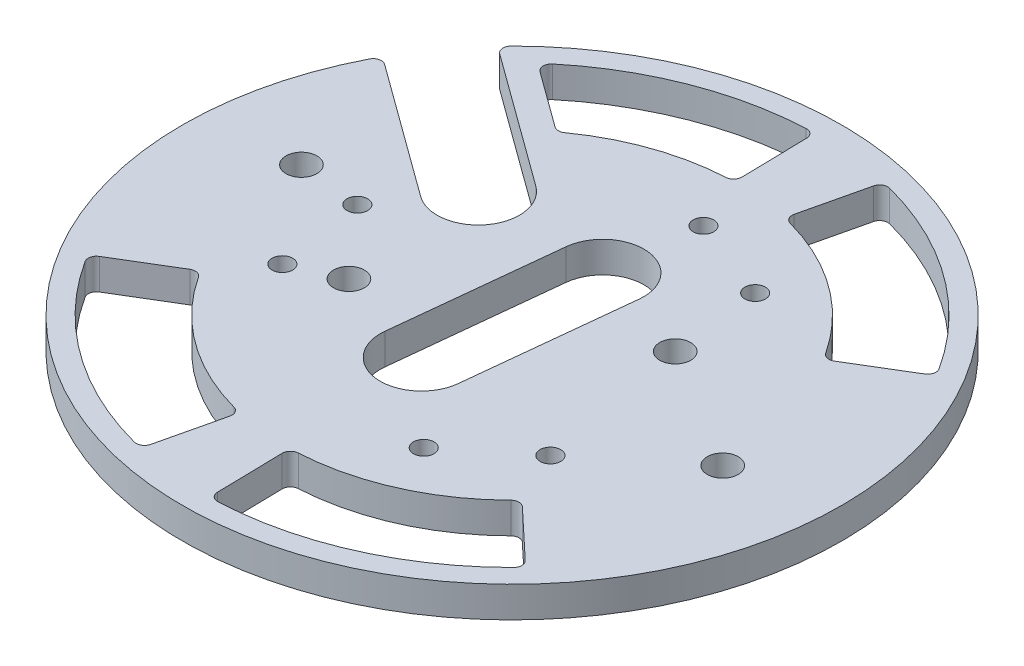
SolidWorks part; units mm, degrees
ref_plane "Front Plane" through (0, 0, 0) normal (0, 0, 1) x (1, 0, 0)
ref_plane "Top Plane" through (0, 0, 0) normal (0, 1, 0) x (1, 0, 0)
ref_plane "Right Plane" through (0, 0, 0) normal (1, 0, 0) x (0, 0, -1)
sketch "Sketch1" plane through (0, 0, 0) normal (0, 1, 0) x (1, 0, 0)
  circle A0 centre (0, 0) radius 101.6
extrude "Boss-Extrude1" add sketch "Sketch1" along normal blind 9.525
sketch "Sketch2" plane through (0, 9.525, 0) normal (0, 1, 0) x (1, 0, 0)
  line L0 (0, 0) -> (34.8175, 15.4709)
  line L1 (0, 60.325) -> (12.6294, 58.9882)
  line L2 (0, 60.325) -> (12.6294, 58.9882)
  line L3 (0, 60.325) -> (-1.3368, 47.6956)
  line L4 (12.6294, 58.9882) -> (11.2926, 46.3587)
  line L5 (-1.3368, 47.6956) -> (11.2926, 46.3587)
  line L6 (0, 0) -> (-34.8175, -15.4709)
  line L7 (0, 0) -> (5.6463, 53.3419)
  line L8 (5.6463, 53.3419) -> (6.6842, 63.1472)
  line L9 (6.6842, 63.1472) -> (6.9516, 65.6731)
  line L10 (0, 0) -> (5.6463, 53.3419)
  line L11 (6.6842, 63.1472) -> (6.9516, 65.6731)
  line L12 (6.9516, 65.6731) -> (10.6947, 101.0356)
  line L13 (4.9779, 47.0271) -> (-2.6737, -25.2589)
  line L14 (-2.6737, -25.2589) -> (2.6737, 25.2589) construction
  line L15 (-15.3031, -23.922) -> (-9.9558, 26.5957)
  line L16 (9.9558, -26.5957) -> (15.3031, 23.922)
  line L17 (0, 0) -> (5.6463, 53.3419) construction
  line L18 (0, 60.325) -> (11.2926, 46.3587)
  line L19 (12.6294, 58.9882) -> (-1.3368, 47.6956)
  line L20 (0, 0) -> (31.5608, 43.3723) construction
  line L21 (0, 0) -> (-53.3419, 5.6463) construction
  line L22 (0, 0) -> (-43.3723, 31.5608) construction
  line L23 (-48.5068, 35.297) -> (-38.2378, 27.8245) construction
  line L24 (-41.0343, 45.566) -> (-30.7653, 38.0935)
  line L25 (-55.9792, 25.028) -> (-45.7102, 17.5555)
  line L26 (-41.0343, 45.566) -> (-87.237, 79.1864)
  line L27 (-45.7102, 17.5555) -> (-104.486, 60.325)
  line L28 (-104.486, 60.325) -> (-87.237, 79.1864)
  circle A0 centre (0, 0) radius 63.5
  circle A1 centre (0, 0) radius 60.325
  circle A2 centre (0, 0) radius 25.4
  arc A3 (-15.3031, -23.922) -> (9.9558, -26.5957) centre (-2.6737, -25.2589) ccw
  arc A4 (15.3031, 23.922) -> (-9.9558, 26.5957) centre (2.6737, 25.2589) ccw
  circle A5 centre (5.6463, 53.3419) radius 3.175
  circle A6 centre (43.3723, -31.5608) radius 3.175
  circle A7 centre (-49.0186, -21.7811) radius 3.175
  circle A8 centre (0, 0) radius 53.6399
  circle A9 centre (31.5608, 43.3723) radius 3.175
  circle A10 centre (21.7811, -49.0186) radius 3.175
  circle A11 centre (-53.3419, 5.6463) radius 3.175
  circle A12 centre (-43.3723, 31.5608) radius 3.175
  arc A13 (-41.0343, 45.566) -> (-55.9792, 25.028) centre (-48.5068, 35.297) ccw
  arc A14 (-45.7102, 17.5555) -> (-30.7653, 38.0935) centre (-38.2378, 27.8245) ccw
  circle A17 centre (0, 0) radius 38.1
  circle A18 centre (-34.8175, -15.4709) radius 4.7625
  circle A19 centre (34.8175, 15.4709) radius 4.7625
  circle A20 centre (0, 0) radius 101.6 construction
  circle A21 centre (10.6947, 101.0356) radius 35.56
  circle A22 centre (-10.6947, -101.0356) radius 35.56
  point P11 (0, 0)
  point P20 (0, 0)
  point P38 (0, 0)
  point P39 (0, 0)
  point P40 (-43.3723, 31.5608)
  point P43 (0, 0)
  point P46 (0, 0)
  point P51 (0, 0)
  point P55 (0, 0)
  point P62 (0, 0)
  point P73 (0, 0)
  circle M1 centre (0, 0) radius 101.6
  dimension "D1" = 3
  dimension "D2" = 2
  dimension "D3" = 2
  dimension "D4" = 30
  dimension "D7" = 30
  dimension "D5" = 3
  dimension "D6" = 2
extrude "Cut-Extrude1" cut sketch "Sketch2" against normal blind 22.86 contours A8 A12 | A8 A12 | A13 A0 L26 L27 M1 | A13 A0 L27 | A13 L26 A0
sketch "Sketch3" plane through (0, 9.525, 0) normal (0, 1, 0) x (1, 0, 0)
  line L0 (0, 0) -> (34.8175, 15.4709)
  line L1 (34.8175, 15.4709) -> (63.8321, 28.3634)
  line L2 (63.8321, 28.3634) -> (87.0438, 38.6774)
  line L3 (0, 0) -> (91.1964, 27.4914)
  line L4 (0, 0) -> (81.5264, 49.2545)
  line L5 (0, 0) -> (69.4065, -65.2327)
  line L6 (0, 0) -> (83.4189, -45.9767)
  line L7 (0, 0) -> (-21.7899, -92.7241)
  line L8 (0, 0) -> (1.8925, -95.2312)
  line L9 (0, 0) -> (-91.1964, -27.4914)
  line L10 (0, 0) -> (-81.5264, -49.2545)
  line L11 (0, 0) -> (-69.4065, 65.2327)
  line L12 (0, 0) -> (-83.4189, 45.9767)
  line L13 (0, 0) -> (21.7899, 92.7241)
  line L14 (0, 0) -> (-1.8925, 95.2312)
  line L15 (-88.9801, 49.0418) -> (-45.7102, 17.5555) construction
  line L17 (-88.9801, 49.0418) -> (-52.4002, 22.4237)
  line L18 (-88.9801, 49.0418) -> (-93.4636, 42.8804)
  line L19 (-52.4002, 22.4237) -> (-56.8837, 16.2623)
  line L20 (-93.4636, 42.8804) -> (-56.8837, 16.2623)
  line L21 (-70.6637, 67.1265) -> (-37.3437, 42.8804)
  line L22 (-70.6637, 67.1265) -> (-66.1802, 73.2879)
  line L23 (-37.3437, 42.8804) -> (-32.8602, 49.0418)
  line L24 (-66.1802, 73.2879) -> (-32.8602, 49.0418)
  line L25 (-74.0352, 69.5798) -> (-30.7653, 38.0935) construction
  line L26 (0, 0) -> (-94.7208, 10.0263)
  circle A0 centre (0, 0) radius 63.5
  circle A1 centre (0, 0) radius 69.85
  circle A2 centre (0, 0) radius 95.25
  circle A3 centre (0, 0) radius 73.025
  circle A4 centre (-72.6193, 7.6868) radius 4.7625
  circle A5 centre (72.6193, -7.6868) radius 4.7625
  point P26 (0, 0)
  point P46 (0, 0)
  dimension "D1" = 6
  dimension "D2" = 2
extrude "Cut-Extrude2" cut sketch "Sketch3" against normal through all
fillet "Fillet1" radius 2.54 2 edges at (-74.0352, 4.7625, -69.5798) (-88.9801, 4.7625, -49.0418)
fillet "Fillet3" radius 2.54 16 edges at (-59.786, 4.7625, 36.12) (-81.5264, 4.7625, 49.2545) (-15.9793, 4.7625, 67.9977) (-21.7899, 4.7625, 92.7241) (1.8925, 4.7625, 95.2312) (1.3878, 4.7625, 69.8362) (69.4065, 4.7625, 65.2327) (50.8981, 4.7625, 47.8373) (59.786, 4.7625, -36.12) (81.5264, 4.7625, -49.2545) (21.7899, 4.7625, -92.7241) (15.9793, 4.7625, -67.9977) (-1.8925, 4.7625, -95.2312) (-1.3878, 4.7625, -69.8362) (-42.0809, 4.7625, -55.7515) (-63.2886, 4.7625, -71.1837)
